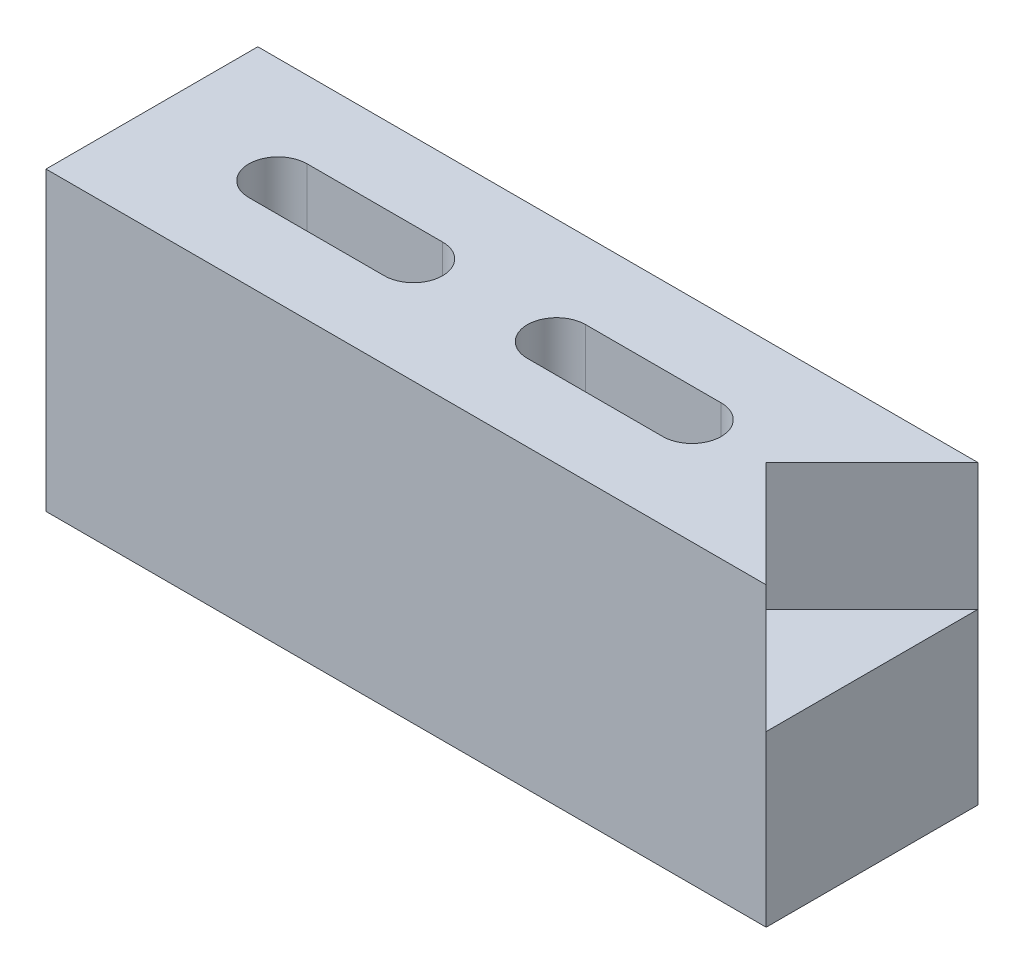
SolidWorks part; units mm, degrees
ref_plane "Front Plane" through (0, 0, 0) normal (0, 0, 1) x (1, 0, 0)
ref_plane "Top Plane" through (0, 0, 0) normal (0, 1, 0) x (1, 0, 0)
ref_plane "Right Plane" through (0, 0, 0) normal (1, 0, 0) x (0, 0, -1)
sketch "Sketch1" plane through (0, 0, 0) normal (0, 0, 1) x (1, 0, 0)
  line L0 (0, 0) -> (43.18, 0)
  line L6 (0, 0) -> (0, 17.78)
  line L10 (0, 17.78) -> (43.18, 17.78)
  line L11 (43.18, 0) -> (43.18, 17.78)
  dimension "D1" = 43.18
  dimension "D2" = 17.78
extrude "Boss-Extrude1" add sketch "Sketch1" against normal blind 12.7
sketch "Sketch3" plane through (0, 17.78, 0) normal (0, 1, 0) x (1, 0, 0)
  line L0 (43.18, 12.7) -> (36.83, 6.35)
  line L1 (36.83, 6.35) -> (43.18, 0)
  line L4 (43.18, 12.7) -> (43.18, 0)
  dimension "D2" = 90
extrude "Cut-Extrude1" cut sketch "Sketch3" against normal blind 7.62
sketch "Sketch4" plane through (0, 17.78, 0) normal (0, 1, 0) x (1, 0, 0)
  line L0 (32.381, 6.35) -> (24.261, 6.35) construction
  line L1 (32.381, 4.6) -> (24.261, 4.6)
  line L2 (32.381, 8.1) -> (24.261, 8.1)
  line L3 (15.681, 6.35) -> (7.561, 6.35) construction
  line L4 (15.681, 4.6) -> (7.561, 4.6)
  line L5 (15.681, 8.1) -> (7.561, 8.1)
  line L6 (43.18, 0) -> (0, 0) construction
  line L7 (0, 12.7) -> (0, 0) construction
  arc A0 (32.381, 4.6) -> (32.381, 8.1) centre (32.381, 6.35) ccw
  arc A1 (24.261, 8.1) -> (24.261, 4.6) centre (24.261, 6.35) ccw
  arc A2 (15.681, 4.6) -> (15.681, 8.1) centre (15.681, 6.35) ccw
  arc A3 (7.561, 8.1) -> (7.561, 4.6) centre (7.561, 6.35) ccw
  point P2 (28.321, 6.35)
  point P7 (11.621, 6.35)
  point P14 (34.131, 6.35)
  point P16 (5.811, 6.35)
  point P18 (17.431, 6.35)
  point P19 (22.511, 6.35)
  dimension "D1" = 1.75
  dimension "D2" = 2.699
  dimension "D3" = 5.811
  dimension "D4" = 6.35
  dimension "D5" = 5.08
extrude "Cut-Extrude2" cut sketch "Sketch4" against normal through all
